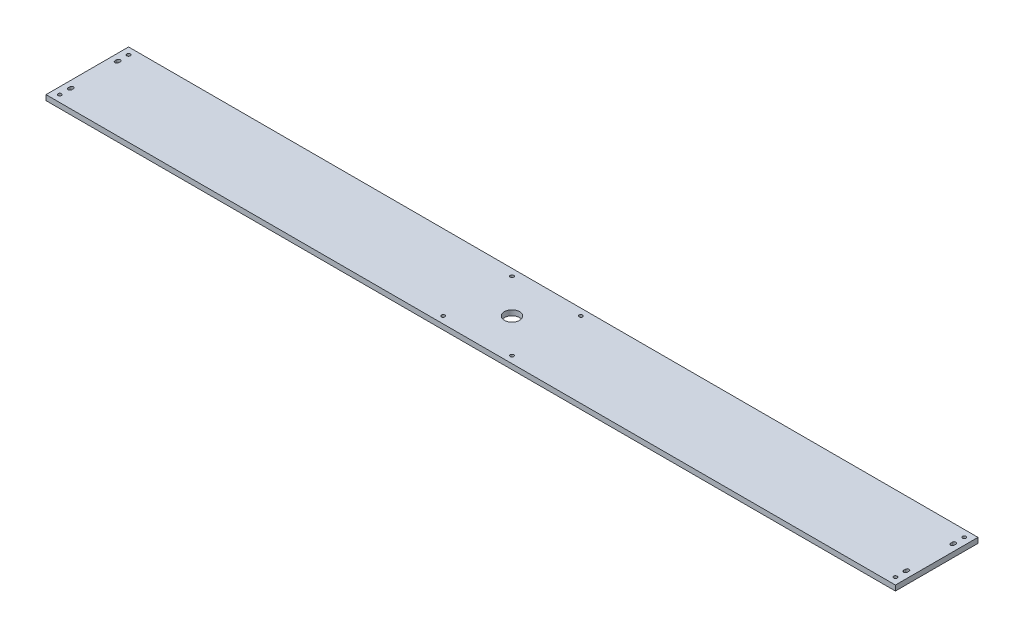
SolidWorks part; units mm, degrees
ref_plane "Front Plane" through (0, 0, 0) normal (0, 0, 1) x (1, 0, 0)
ref_plane "Top Plane" through (0, 0, 0) normal (0, 1, 0) x (1, 0, 0)
ref_plane "Right Plane" through (0, 0, 0) normal (1, 0, 0) x (0, 0, -1)
sketch "Sketch1" plane through (0, 0, 0) normal (0, 1, 0) x (1, 0, 0)
  line L0 (0.5751, 374.8724) -> (0.5751, -160.9245) construction
  line L1 (-783.1419, 30.7739) -> (784.2921, 30.7739)
  line L2 (-783.1419, 30.7739) -> (-783.1419, 183.1739)
  line L3 (-783.1419, 183.1739) -> (784.2921, 183.1739)
  line L4 (784.2921, 30.7739) -> (784.2921, 183.1739)
  line L5 (-783.1419, 30.7739) -> (784.2921, 183.1739) construction
  line L6 (-783.1419, 183.1739) -> (784.2921, 30.7739) construction
  line L7 (-1004.116, 106.9739) -> (1005.2662, 106.9739) construction
  point P0 (0.5751, 106.9739)
  dimension "D1" = 1567.434
  dimension "D2" = 152.4
extrude "Boss-Extrude1" add sketch "Sketch1" along normal blind 9.652
sketch "Sketch2" plane through (0, 9.652, 0) normal (0, 1, 0) x (1, 0, 0)
  line L0 (784.2921, 183.1739) -> (-783.1419, 183.1739) construction
  line L1 (-783.1419, 183.1739) -> (-783.1419, 30.7739) construction
  line L2 (-770.4419, 148.5029) -> (-770.4419, 151.8049) construction
  line L3 (-773.7439, 148.5029) -> (-773.7439, 151.8049)
  line L4 (-767.1399, 148.5029) -> (-767.1399, 151.8049)
  line L5 (-1015.6615, 106.9739) -> (993.7207, 106.9739) construction
  line L9 (-1004.116, 106.9739) -> (1005.2662, 106.9739) construction
  line L10 (0.5751, 410.0083) -> (0.5751, -207.3231) construction
  line L11 (0.5751, 374.8724) -> (0.5751, -160.9245) construction
  line L12 (-770.4419, 65.4449) -> (-770.4419, 62.1429) construction
  line L13 (-773.7439, 65.4449) -> (-773.7439, 62.1429)
  line L14 (-767.1399, 65.4449) -> (-767.1399, 62.1429)
  line L15 (771.5921, 65.4449) -> (771.5921, 62.1429) construction
  line L16 (774.8941, 65.4449) -> (774.8941, 62.1429)
  line L17 (768.2901, 65.4449) -> (768.2901, 62.1429)
  line L18 (771.5921, 148.5029) -> (771.5921, 151.8049) construction
  line L19 (774.8941, 148.5029) -> (774.8941, 151.8049)
  line L20 (768.2901, 148.5029) -> (768.2901, 151.8049)
  line L21 (-783.1419, 183.1739) -> (784.2921, 183.1739) construction
  circle A0 centre (-770.4419, 170.4739) radius 3.175
  arc A1 (-773.7439, 148.5029) -> (-767.1399, 148.5029) centre (-770.4419, 148.5029) ccw
  arc A2 (-767.1399, 151.8049) -> (-773.7439, 151.8049) centre (-770.4419, 151.8049) ccw
  arc A3 (-773.7439, 65.4449) -> (-767.1399, 65.4449) centre (-770.4419, 65.4449) cw
  arc A4 (-767.1399, 62.1429) -> (-773.7439, 62.1429) centre (-770.4419, 62.1429) cw
  circle A5 centre (-770.4419, 43.4739) radius 3.175
  circle A6 centre (771.5921, 43.4739) radius 3.175
  arc A7 (774.8941, 65.4449) -> (768.2901, 65.4449) centre (771.5921, 65.4449) ccw
  arc A8 (768.2901, 62.1429) -> (774.8941, 62.1429) centre (771.5921, 62.1429) ccw
  arc A9 (774.8941, 148.5029) -> (768.2901, 148.5029) centre (771.5921, 148.5029) cw
  arc A10 (768.2901, 151.8049) -> (774.8941, 151.8049) centre (771.5921, 151.8049) cw
  circle A11 centre (771.5921, 170.4739) radius 3.175
  circle A12 centre (0.5751, 106.9739) radius 13.97
  circle A13 centre (-62.9249, 170.4739) radius 3.175
  circle A14 centre (-62.9249, 43.4739) radius 3.175
  circle A15 centre (64.0751, 43.4739) radius 3.175
  circle A16 centre (64.0751, 170.4739) radius 3.175
  point P8 (-770.4419, 150.1539)
  point P23 (-770.4419, 63.7939)
  point P34 (771.5921, 63.7939)
  point P41 (771.5921, 150.1539)
  dimension "D1" = 6.35
  dimension "D5" = 3.302
  dimension "D7" = 27.94
  dimension "D8" = 6.35
  dimension "D2" = 12.7
  dimension "D3" = 12.7
  dimension "D4" = 3.302
  dimension "D6" = 20.32
  dimension "D9" = 63.5
  dimension "D10" = 12.7
extrude "Cut-Extrude2" cut sketch "Sketch2" against normal through all
